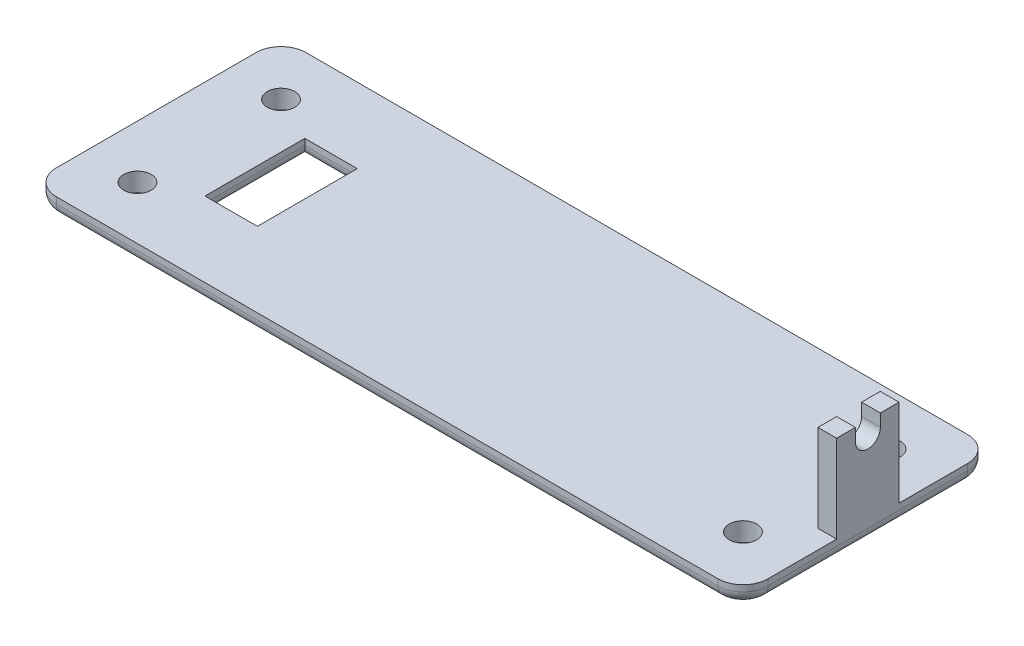
SolidWorks part; units mm, degrees
ref_plane "Front Plane" through (0, 0, 0) normal (0, 0, 1) x (1, 0, 0)
ref_plane "Top Plane" through (0, 0, 0) normal (0, 1, 0) x (1, 0, 0)
ref_plane "Right Plane" through (0, 0, 0) normal (1, 0, 0) x (0, 0, -1)
sketch "Sketch1" plane through (0, 0, 0) normal (0, 1, 0) x (1, 0, 0)
  line L1 (-72.39, -25.4) -> (72.39, -25.4)
  line L2 (-72.39, -25.4) -> (-72.39, 25.4)
  line L3 (-72.39, 25.4) -> (72.39, 25.4)
  line L4 (72.39, -25.4) -> (72.39, 25.4)
  line L5 (-72.39, -25.4) -> (72.39, 25.4) construction
  line L6 (-72.39, 25.4) -> (72.39, -25.4) construction
  point P0 (0, 0)
  dimension "D1" = 144.78
  dimension "D2" = 50.8
extrude "Boss-Extrude1" add sketch "Sketch1" along normal blind 3.81
sketch "Sketch2" plane through (0, 3.81, 0) normal (0, 1, 0) x (1, 0, 0)
  line L0 (72.39, -25.4) -> (72.39, 25.4) construction
  line L1 (72.39, 6.35) -> (68.58, 6.35)
  line L2 (72.39, 6.35) -> (72.39, -6.35)
  line L3 (72.39, -6.35) -> (68.58, -6.35)
  line L4 (68.58, 6.35) -> (68.58, -6.35)
  line L5 (72.39, 6.35) -> (68.58, 6.35) construction
extrude "Boss-Extrude2" add sketch "Sketch2" along normal blind 17.78
sketch "Sketch3" plane through (72.39, 0, 0) normal (1, 0, 0) x (0, 0, -1)
  line L0 (-2.54, 21.59) -> (2.54, 21.59)
  line L1 (-2.54, 21.59) -> (-2.54, 19.05)
  line L2 (2.54, 21.59) -> (2.54, 19.05)
  line L5 (-6.35, 21.59) -> (6.35, 21.59) construction
  arc A0 (2.54, 19.05) -> (-2.54, 19.05) centre (0, 19.05) cw
  point P5 (0, 21.59)
  dimension "D1" = 5.08
  dimension "D2" = 2.54
extrude "Cut-Extrude1" cut sketch "Sketch3" against normal up to next
sketch "Sketch4" plane through (0, 0, 0) normal (0, -1, 0) x (1, 0, 0)
  line L0 (-52.31, 25.4) -> (-52.31, -25.4) construction
  line L1 (-72.39, 25.4) -> (72.39, 25.4) construction
  line L2 (72.39, -25.4) -> (-72.39, -25.4) construction
  line L3 (-72.39, -25.4) -> (-72.39, 25.4) construction
  line L4 (-41.642, 25.4) -> (-41.642, -25.4) construction
  line L5 (-52.31, 0) -> (-41.642, 0) construction
  line L7 (-41.642, -10.16) -> (-52.31, -10.16)
  line L8 (-41.642, -10.16) -> (-41.642, 10.16)
  line L9 (-41.642, 10.16) -> (-52.31, 10.16)
  line L10 (-52.31, -10.16) -> (-52.31, 10.16)
  line L11 (-41.642, -10.16) -> (-52.31, 10.16) construction
  line L12 (-41.642, 10.16) -> (-52.31, -10.16) construction
  point P12 (-46.976, 0)
  dimension "D1" = 10.668
  dimension "D2" = 20.08
  dimension "D3" = 20.32
extrude "Cut-Extrude2" cut sketch "Sketch4" against normal through all
sketch "Sketch5" plane through (0, 0, 0) normal (0, -1, 0) x (1, 0, 0)
  line L0 (0, 25.4) -> (0, -25.4) construction
  line L1 (-72.39, 25.4) -> (72.39, 25.4) construction
  line L2 (72.39, -25.4) -> (-72.39, -25.4) construction
  line L3 (0, 0) -> (72.39, 0) construction
  line L5 (72.39, 25.4) -> (72.39, -25.4) construction
  circle A1 centre (61.595, -14.605) radius 2.794
  circle A2 centre (61.595, 14.605) radius 2.794
  circle A3 centre (-61.595, 14.605) radius 2.794
  circle A4 centre (-61.595, -14.605) radius 2.794
  dimension "D1" = 5.588
  dimension "D2" = 10.795
  dimension "D3" = 10.795
extrude "Cut-Extrude3" cut sketch "Sketch5" against normal through all
fillet "Fillet3" radius 5.08 4 edges at (-72.39, 1.905, -25.4) (-72.39, 1.905, 25.4) (72.39, 1.905, 25.4) (72.39, 1.905, -25.4)
fillet "Fillet4" radius 2.54 12 edges at (-72.39, 0, 0) (-70.9021, 0, 23.9121) (0, 0, 25.4) (70.9021, 0, 23.9121) (72.39, 0, 0) (70.9021, 0, -23.9121) (0, 0, -25.4) (-46.976, 0, 10.16) (-52.31, 0, 0) (-46.976, 0, -10.16) (-41.642, 0, 0) (-70.9021, 0, -23.9121)
